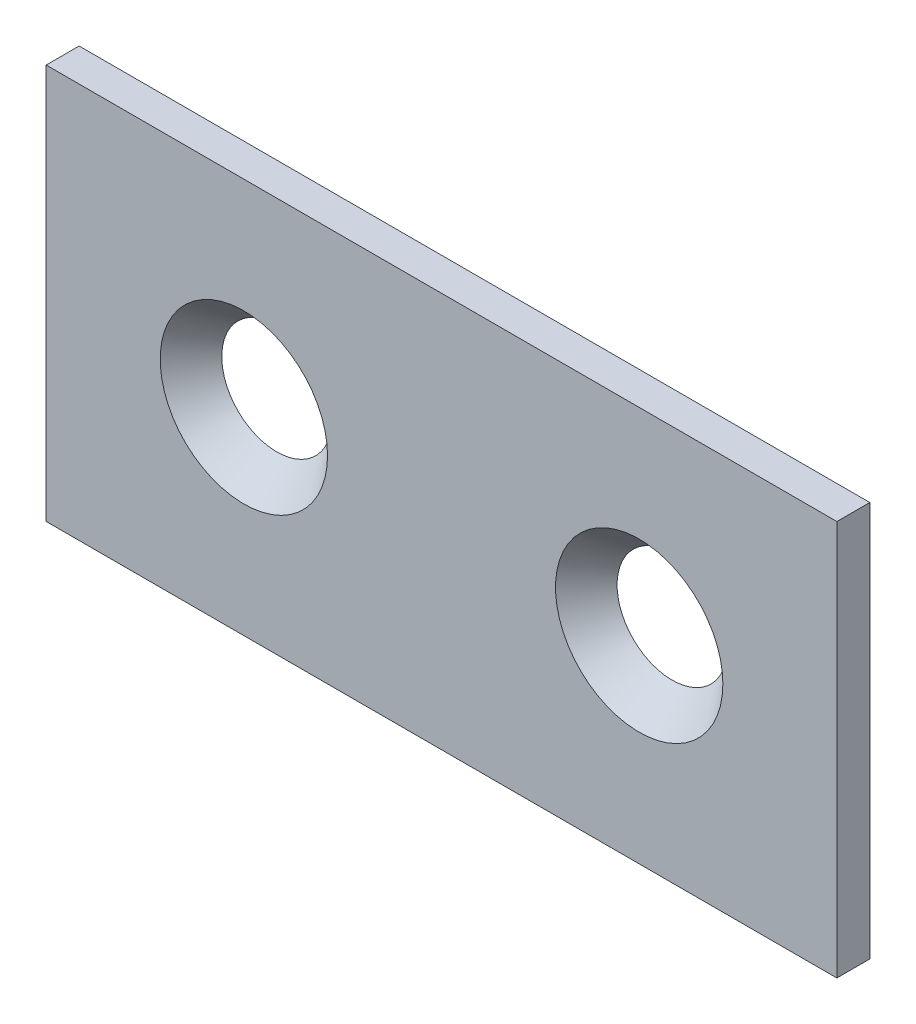
SolidWorks part; units mm, degrees
ref_plane "Front Plane" through (0, 0, 0) normal (0, 0, 1) x (1, 0, 0)
ref_plane "Top Plane" through (0, 0, 0) normal (0, 1, 0) x (1, 0, 0)
ref_plane "Right Plane" through (0, 0, 0) normal (1, 0, 0) x (0, 0, -1)
sketch "Sketch1" plane through (0, 0, 0) normal (0, 0, 1) x (1, 0, 0)
  line L1 (-38.1, 19.05) -> (38.1, 19.05)
  line L2 (-38.1, 19.05) -> (-38.1, -19.05)
  line L3 (-38.1, -19.05) -> (38.1, -19.05)
  line L4 (38.1, 19.05) -> (38.1, -19.05)
  line L5 (-38.1, 19.05) -> (38.1, -19.05) construction
  line L6 (-38.1, -19.05) -> (38.1, 19.05) construction
  circle A0 centre (-19.05, 0) radius 4.191
  circle A1 centre (19.05, 0) radius 4.1656
  point P0 (0, 0)
  dimension "D3" = 8.3312
  dimension "D4" = 8.382
  dimension "D1" = 76.2
  dimension "D2" = 38.1
  dimension "D5" = 38.1
  dimension "D6" = 19.05
extrude "Boss-Extrude1" add sketch "Sketch1" against normal blind 3.175
hole_wizard "CSK for 5/16 Flat Head Machine Screw2" positions "3DSketch1" profile "Sketch2" countersink size "5/16" standard "ANSI Inch"
sketch3d "3DSketch1"
  line L0 (-19.05, 0, -3.175) -> (-19.05, 0, 0) construction
  line L1 (19.05, 0, -3.175) -> (19.05, 0, 0) construction
  circle A0 centre (-19.05, 0, 0) radius 4.191 construction
  point P0 (-16.455, 3.2909, 0)
  point P4 (-19.05, 0, 4.191)
  point P5 (-19.05, 0, 0)
  point P9 (19.05, 0, 0)
sketch "Sketch2" plane through (-19.05, 0, 0) normal (1, 0, 0) x (0, -1, 0)
  line L0 (0, 0) -> (0, 35.2995)
  line L1 (0, 35.2995) -> (4.2164, 32.766)
  line L2 (4.2164, 32.766) -> (4.2164, 4.4267)
  line L3 (4.2164, 4.4267) -> (8.0645, 0)
  line L5 (8.0645, 0) -> (0, 0)
  line L6 (-4.2164, 4.4267) -> (-8.0645, 0) construction
  line L10 (0, 35.2995) -> (-4.2164, 32.766) construction
  line L11 (0, -6.35) -> (0, 107.95) construction
  dimension "Hole Dia." = 8.4328
  dimension "Hole Depth" = 32.766
  dimension "Near C'Sink Dia." = 16.129
  dimension "Near C'Sink Angle" = 82
  dimension "Drill Angle" = 118
